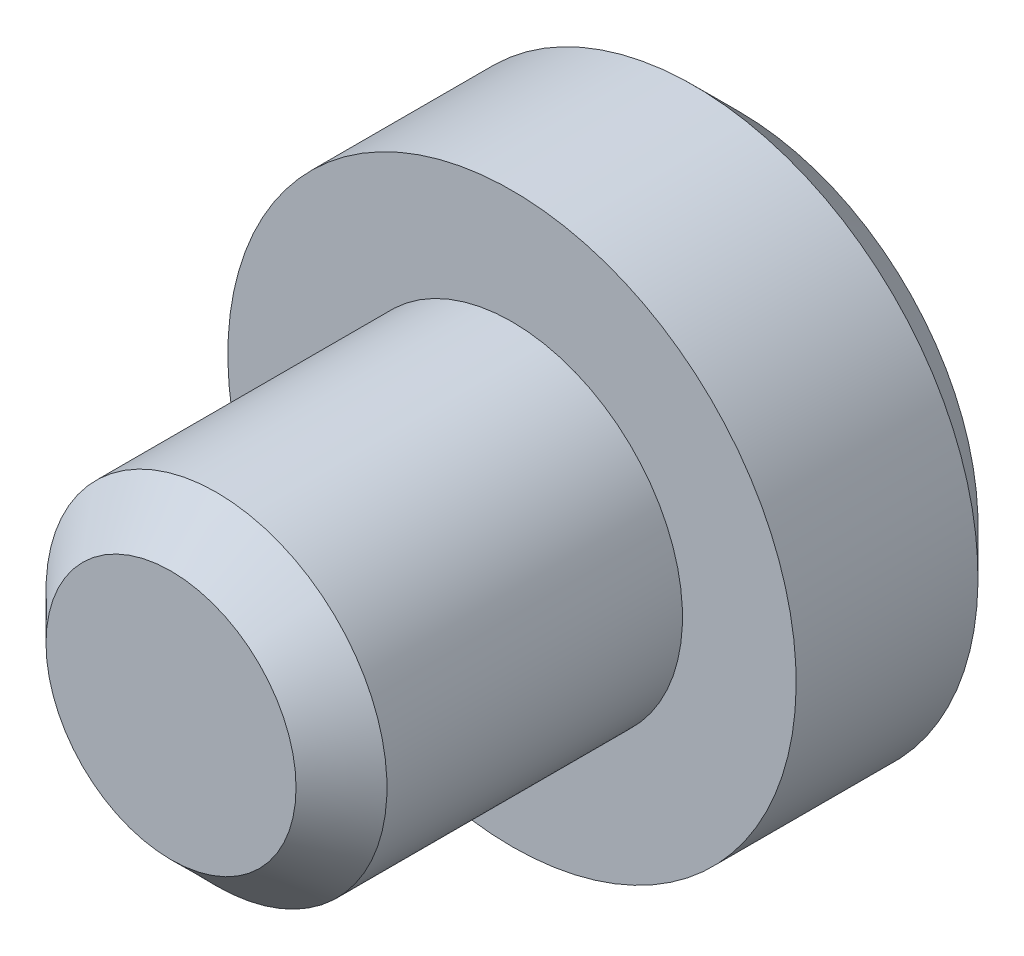
SolidWorks part; units mm, degrees
ref_plane "Front Plane" through (0, 0, 0) normal (0, 0, 1) x (1, 0, 0)
ref_plane "Top Plane" through (0, 0, 0) normal (0, 1, 0) x (1, 0, 0)
ref_plane "Right Plane" through (0, 0, 0) normal (1, 0, 0) x (0, 0, -1)
sketch "Sketch2" plane through (0, 0, 0) normal (1, 0, 0) x (0, 0, -1)
  line L0 (0, 0) -> (-1.4064, 0) construction
  line L1 (0, 0) -> (0, 4893.7954) construction
  line L2 (0, 2.5) -> (-2, 2.5)
  line L3 (-2, 2.5) -> (-2, 1.5)
  line L4 (-2, 1.5) -> (-5, 1.5)
  line L5 (-5, 1.5) -> (-5, 0)
  line L6 (-5, 0) -> (0, 0)
  line L7 (0, 0) -> (0, 2.5)
  dimension "D1" = 2
  dimension "D2" = 1.5
  dimension "D3" = 2.5
  dimension "D4" = 3
revolve "Revolve1" add sketch "Sketch2" angle 360 about L6
sketch "Sketch3" plane through (0, 0, 0) normal (0, 0, -1) x (-1, 0, 0)
  line L1 (1.1684, -0.4981) -> (1.0156, 0.7629)
  line L2 (1.0156, 0.7629) -> (-0.1529, 1.2609)
  line L3 (-0.1529, 1.2609) -> (-1.1684, 0.4981)
  line L4 (-1.1684, 0.4981) -> (-1.0156, -0.7629)
  line L5 (-1.0156, -0.7629) -> (0.1529, -1.2609)
  line L6 (0.1529, -1.2609) -> (1.1684, -0.4981)
  circle A1 centre (0, 0) radius 1.1 construction
  dimension "D1" = 2.2
extrude "Cut-Extrude1" cut sketch "Sketch3" against normal blind 2
chamfer "Chamfer1" distance 0.4 angle 45 2 edges at (0, -1.5, 5) (0, -2.5, 0)
chamfer "Chamfer2" distance 0.1 angle 45 6 edges at (0.4313, -1.0119, 0) (1.092, -0.1324, 0) (0.6607, 0.8795, 0) (-0.4313, 1.0119, 0) (-1.092, 0.1324, 0) (-0.6607, -0.8795, 0)
